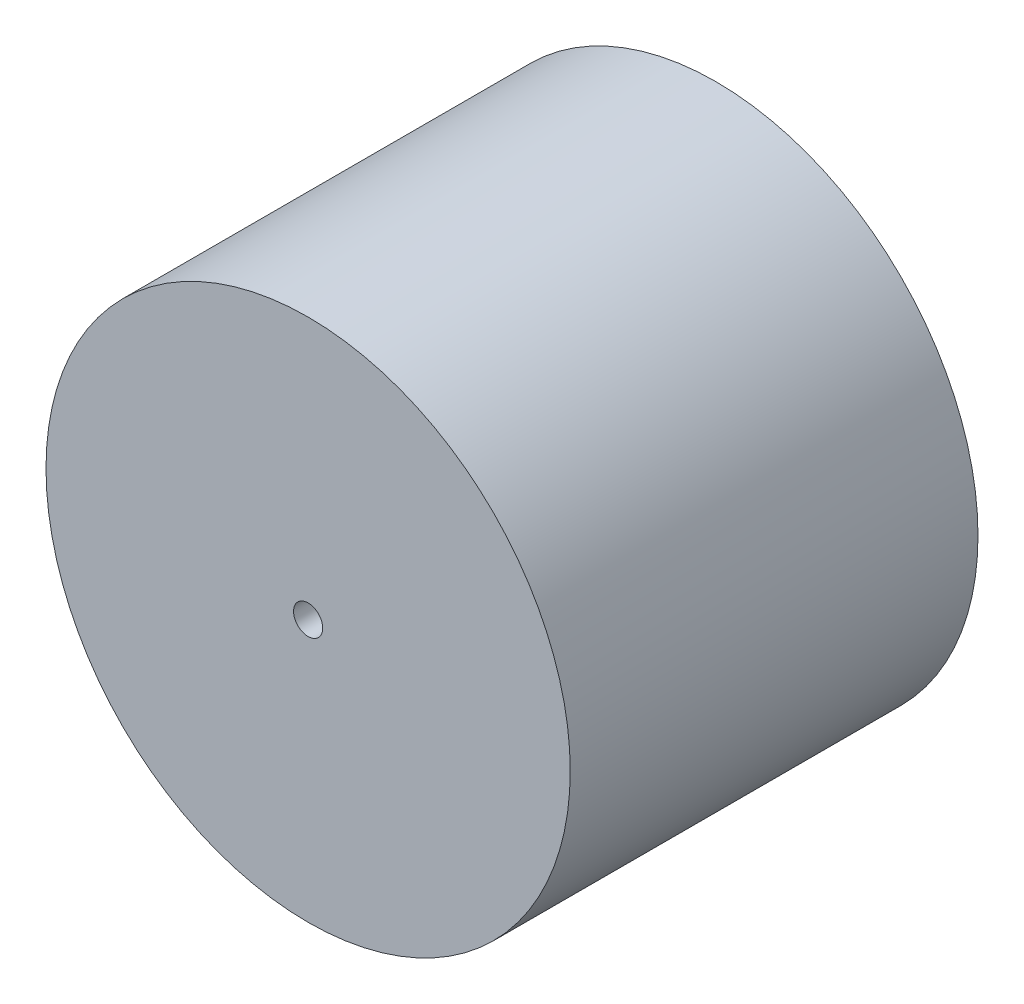
SolidWorks part; units mm, degrees
ref_plane "Front Plane" through (0, 0, 0) normal (0, 0, 1) x (1, 0, 0)
ref_plane "Top Plane" through (0, 0, 0) normal (0, 1, 0) x (1, 0, 0)
ref_plane "Right Plane" through (0, 0, 0) normal (1, 0, 0) x (0, 0, -1)
sketch "Sketch1" plane through (0, 0, 0) normal (0, 0, 1) x (1, 0, 0)
  circle A0 centre (-19.4471, 20.52) radius 9
  dimension "D1" = 18
extrude "Boss-Extrude1" add sketch "Sketch1" along normal mid plane 14
sketch "Sketch2" plane through (0, 0, 7) normal (0, 0, 1) x (1, 0, 0)
  circle A0 centre (-19.4471, 20.52) radius 0.5
  dimension "D1" = 1
extrude "Cut-Extrude1" cut sketch "Sketch2" against normal blind 14
